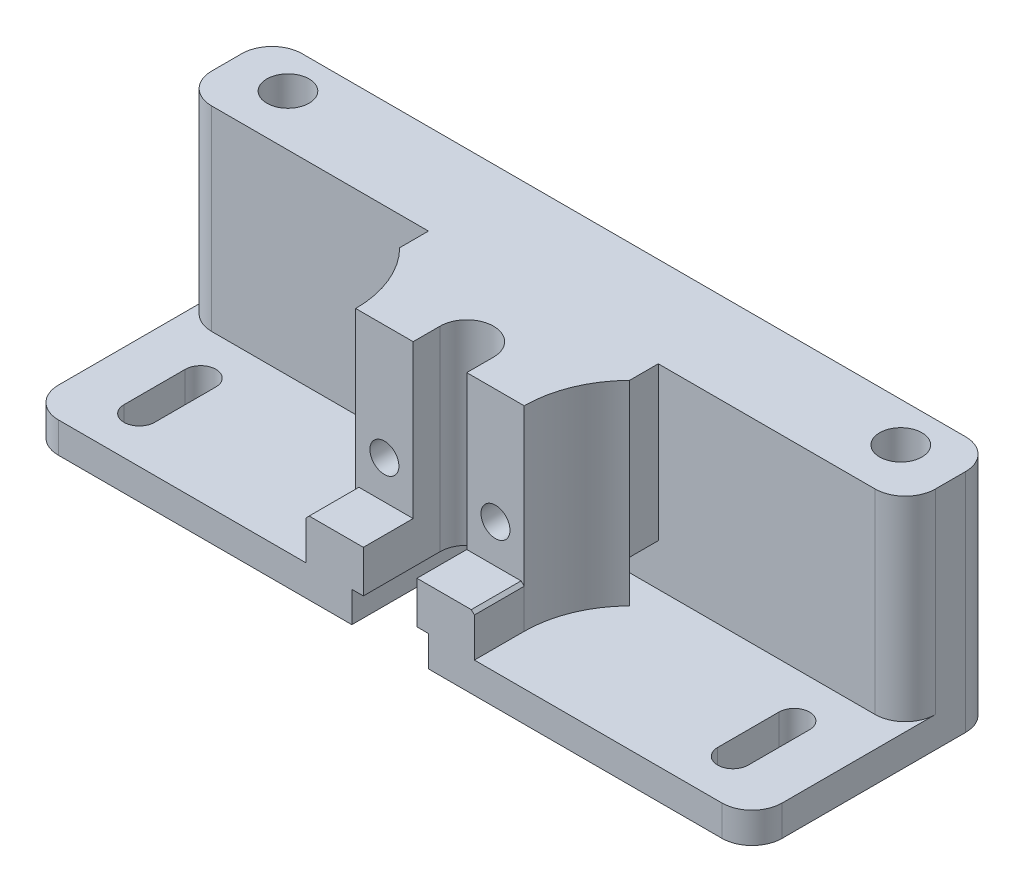
SolidWorks part; units mm, degrees
ref_plane "Front Plane" through (0, 0, 0) normal (0, 0, 1) x (1, 0, 0)
ref_plane "Top Plane" through (0, 0, 0) normal (0, 1, 0) x (1, 0, 0)
ref_plane "Right Plane" through (0, 0, 0) normal (1, 0, 0) x (0, 0, -1)
ref_plane "Plane1" through (0, 0, -20.6375) normal (0, 0, -1) x (-1, 0, 0)
sketch "Sketch1" plane through (0, 0, -20.6375) normal (0, 0, -1) x (-1, 0, 0)
  line L0 (19.05, 0) -> (19.05, 25.4)
  line L1 (19.05, 25.4) -> (-19.05, 25.4)
  line L2 (-19.05, 25.4) -> (-19.05, 0)
  line L3 (-19.05, 0) -> (19.05, 0)
extrude "Boss-Extrude1" add sketch "Sketch1" against normal blind 25.0825
ref_plane "Plane2" through (0, 0, -2.2225) normal (0, 0, 1) x (1, 0, 0)
ref_plane "Plane3" through (0, 0, 0) normal (0, -1, 0) x (-1, 0, 0)
sketch "Sketch18" plane through (0, 0, 0) normal (0, -1, 0) x (-1, 0, 0)
  line L0 (13.97, -4.445) -> (19.05, -4.445)
  line L1 (19.05, -4.445) -> (19.05, 7.9375)
  arc A0 (19.05, 7.9375) -> (13.97, -4.445) centre (31.6012, -4.445) ccw
extrude "Cut-Extrude3" cut sketch "Sketch18" against normal through all
sketch "Sketch19" plane through (0, 0, 0) normal (0, -1, 0) x (1, 0, 0)
  line L0 (4.445, 4.445) -> (-4.445, 4.445)
  line L1 (-4.445, 4.445) -> (-4.445, 0)
  line L2 (4.445, 0) -> (4.445, 4.445)
  arc A0 (-4.445, 0) -> (4.445, 0) centre (0, 0) ccw
extrude "Cut-Extrude4" cut sketch "Sketch19" against normal through all
sketch "Sketch20" plane through (0, 0, 0) normal (0, -1, 0) x (1, 0, 0)
  line L0 (19.05, -7.9375) -> (19.05, 4.445)
  line L1 (19.05, 4.445) -> (13.97, 4.445)
  arc A0 (13.97, 4.445) -> (19.05, -7.9375) centre (31.6012, 4.445) ccw
extrude "Cut-Extrude5" cut sketch "Sketch20" against normal through all
sketch "Sketch21" plane through (0, 0, 0) normal (0, -1, 0) x (1, 0, 0)
  line L0 (4.445, 0) -> (4.445, 12.7)
  line L1 (4.445, 12.7) -> (13.97, 12.7)
  line L2 (13.97, 12.7) -> (13.97, 4.445)
  line L3 (19.05, -7.9375) -> (-19.05, -7.9375)
  line L4 (-13.97, 4.445) -> (-13.97, 12.7)
  line L5 (-13.97, 12.7) -> (-4.445, 12.7)
  line L6 (-4.445, 12.7) -> (-4.445, 0)
  arc A0 (13.97, 4.445) -> (19.05, -7.9375) centre (31.6012, 4.445) ccw
  arc A1 (-19.05, -7.9375) -> (-13.97, 4.445) centre (-31.6012, 4.445) ccw
  arc A2 (-4.445, 0) -> (4.445, 0) centre (0, 0) ccw
extrude "Boss-Extrude2" add sketch "Sketch21" along normal blind 6.985
sketch "Sketch22" plane through (0, -6.985, 0) normal (0, -1, 0) x (1, 0, 0)
  line L0 (-4.445, -6.35) -> (4.445, -6.35)
  line L1 (4.445, -6.35) -> (4.445, 12.7)
  line L2 (4.445, 12.7) -> (60, 12.7)
  line L3 (60, 12.7) -> (60, -12.7)
  line L4 (60, -12.7) -> (-60, -12.7)
  line L5 (-60, -12.7) -> (-60, 12.7)
  line L6 (-60, 12.7) -> (-4.445, 12.7)
  line L7 (-4.445, 12.7) -> (-4.445, -6.35)
  point P8 (0, -12.7)
  dimension "D1" = 25.4
  dimension "D2" = 120
  dimension "D3" = 8.89
  dimension "D4" = 4.445
extrude "Boss-Extrude3" add sketch "Sketch22" along normal blind 5.08
ref_plane "Plane4" through (4.445, 0, 0) normal (-1, 0, 0) x (0, 0, 1)
sketch "Sketch29" plane through (4.445, 0, 0) normal (-1, 0, 0) x (0, 0, 1)
  line L0 (12.7, -6.985) -> (-6.35, -6.985)
  line L1 (-6.35, -6.985) -> (-6.35, -12.065)
  line L2 (-6.35, -12.065) -> (12.7, -12.065)
  line L3 (12.7, -12.065) -> (12.7, -6.985)
extrude "Cut-Extrude6" cut sketch "Sketch29" against normal blind 1.905
sketch "Sketch30" plane through (-4.445, 0, 0) normal (1, 0, 0) x (0, 0, -1)
  line L0 (-12.7, -6.985) -> (-12.7, -12.065)
  line L1 (-12.7, -12.065) -> (6.35, -12.065)
  line L2 (6.35, -12.065) -> (6.35, -6.985)
  line L3 (6.35, -6.985) -> (-12.7, -6.985)
extrude "Cut-Extrude7" cut sketch "Sketch30" against normal blind 1.905
ref_plane "Plane5" through (0, -12.065, 0) normal (0, -1, 0) x (-1, 0, 0)
sketch "Sketch48" plane through (0, -12.065, 0) normal (0, -1, 0) x (-1, 0, 0)
  line L0 (-51.7525, 5.08) -> (-51.7525, -5.08)
  line L1 (-46.6725, -5.08) -> (-46.6725, 5.08)
  arc A0 (-46.6725, 5.08) -> (-51.7525, 5.08) centre (-49.2125, 5.08) ccw
  arc A1 (-51.7525, -5.08) -> (-46.6725, -5.08) centre (-49.2125, -5.08) ccw
extrude "Cut-Extrude10" cut sketch "Sketch48" against normal up to next
sketch "Sketch57" plane through (0, -12.065, 0) normal (0, -1, 0) x (-1, 0, 0)
  line L0 (46.6725, 5.08) -> (46.6725, -5.08)
  line L1 (51.7525, -5.08) -> (51.7525, 5.08)
  arc A0 (51.7525, 5.08) -> (46.6725, 5.08) centre (49.2125, 5.08) ccw
  arc A1 (46.6725, -5.08) -> (51.7525, -5.08) centre (49.2125, -5.08) ccw
extrude "Cut-Extrude11" cut sketch "Sketch57" against normal up to next
ref_plane "Plane6" through (0, 6.35, 0) normal (0, 1, 0) x (1, 0, 0)
sketch "Sketch67" plane through (0, 6.35, 0) normal (0, 1, 0) x (1, 0, 0)
  line L0 (-7.7343, 20.6375) -> (-9.2075, 20.6375)
  line L1 (-9.2075, 20.6375) -> (-9.2075, 4.6101)
  line L2 (-9.2075, 4.6101) -> (-7.7343, 4.6101)
  line L3 (-7.7343, 4.6101) -> (-7.7343, 20.6375)
  line L4 (-9.2075, 20.6375) -> (-9.2075, 4.6101) construction
sketch "Sketch77" plane through (0, 6.35, 0) normal (0, 1, 0) x (1, 0, 0)
  line L0 (10.6807, 20.6375) -> (9.2075, 20.6375)
  line L1 (9.2075, 20.6375) -> (9.2075, 4.6101)
  line L2 (9.2075, 4.6101) -> (10.6807, 4.6101)
  line L3 (10.6807, 4.6101) -> (10.6807, 20.6375)
  line L4 (9.2075, 20.6375) -> (9.2075, 4.6101) construction
revolve "Cut-Revolve2" cut sketch "Sketch77" angle 360 about L1
hole_wizard "M2.5 Clearance Hole1" positions "Sketch79" profile "Sketch78" hole size "M2.5" standard "ANSI Metric"
sketch "Sketch79" plane through (0, 0, 4.445) normal (0, 0, 1) x (1, 0, 0)
  point P0 (9.2075, 6.35)
  point P1 (-9.2075, 6.35)
sketch "Sketch78" plane through (9.2075, 6.35, 4.445) normal (1, 0, 0) x (0, -1, 0)
  line L0 (0, 0) -> (0, 25.0825)
  line L1 (0, 25.0825) -> (1.4732, 25.0825)
  line L2 (1.4732, 25.0825) -> (1.4732, 0)
  line L5 (1.4732, 0) -> (0, 0)
  line L11 (0, -6.35) -> (0, 107.95) construction
  dimension "Thru Hole Dia." = 2.9464
  dimension "Thru Hole Depth" = 25.0825
chamfer "Chamfer1" distance 0.5111 angle 45.61 1 edges at (13.97, 0, 8.5725)
chamfer "Chamfer2" distance 0.5582 angle 43.977 1 edges at (-13.97, 0, 8.5725)
sketch "Sketch80" plane through (0, 0, -20.6375) normal (0, 0, -1) x (-1, 0, 0)
  line L0 (-19.05, 25.4) -> (19.05, 25.4)
  line L1 (-19.05, 25.4) -> (-19.05, 0)
  line L2 (-19.05, 0) -> (19.05, 0)
  line L3 (19.05, 25.4) -> (19.05, 0)
extrude "Cut-Extrude13" cut sketch "Sketch80" against normal up to surface (7.9375 mm away) up to face at (0, -9.525, -12.7)
sketch "Sketch81" plane through (0, 25.4, 0) normal (0, 1, 0) x (1, 0, 0)
  line L0 (-19.05, 12.7) -> (19.05, 12.7) construction
  line L1 (60, 12.7) -> (-60, 12.7)
  line L2 (60, 12.7) -> (60, 27.7)
  line L3 (60, 27.7) -> (-60, 27.7)
  line L4 (-60, 12.7) -> (-60, 27.7)
  line L5 (-60, 12.7) -> (60, 12.7) construction
  point P0 (0, 12.7)
  point P7 (0, 12.7)
  dimension "D1" = 120
  dimension "D2" = 15
extrude "Boss-Extrude4" add sketch "Sketch81" against normal up to surface (37.465 mm away) up to face at (-49.2125, -12.065, 0)
sketch "Sketch82" plane through (0, -12.065, 0) normal (0, -1, 0) x (1, 0, 0)
  line L0 (-42.1371, -21.1564) -> (42.1371, -21.1564) construction
  circle A0 centre (-50.8, -21.1564) radius 3.5
  circle A1 centre (50.8, -21.1564) radius 3.5
  point P3 (0, -21.1564)
  dimension "D1" = 50.8
  dimension "D3" = 7
  dimension "D4" = 7
  dimension "D2" = 50.8
extrude "Cut-Extrude14" cut sketch "Sketch82" against normal through all
fillet "Fillet3" radius 5 2 edges at (60, 6.6675, -27.7) (-60, 6.6675, -27.7)
fillet "Fillet4" radius 5 2 edges at (-60, 9.2075, -12.7) (60, 9.2075, -12.7)
fillet "Fillet5" radius 5 2 edges at (60, -9.525, 12.7) (-60, -9.525, 12.7)
sketch "Sketch83" plane through (0, 0, 4.445) normal (0, 0, 1) x (1, 0, 0)
  circle A0 centre (-9.2075, 6.35) radius 2.4003
  circle A1 centre (9.2075, 6.35) radius 2.4003
  dimension "D1" = 4.8006
  dimension "D2" = 4.8006
extrude "Cut-Extrude15" cut sketch "Sketch83" against normal blind 7.1374
